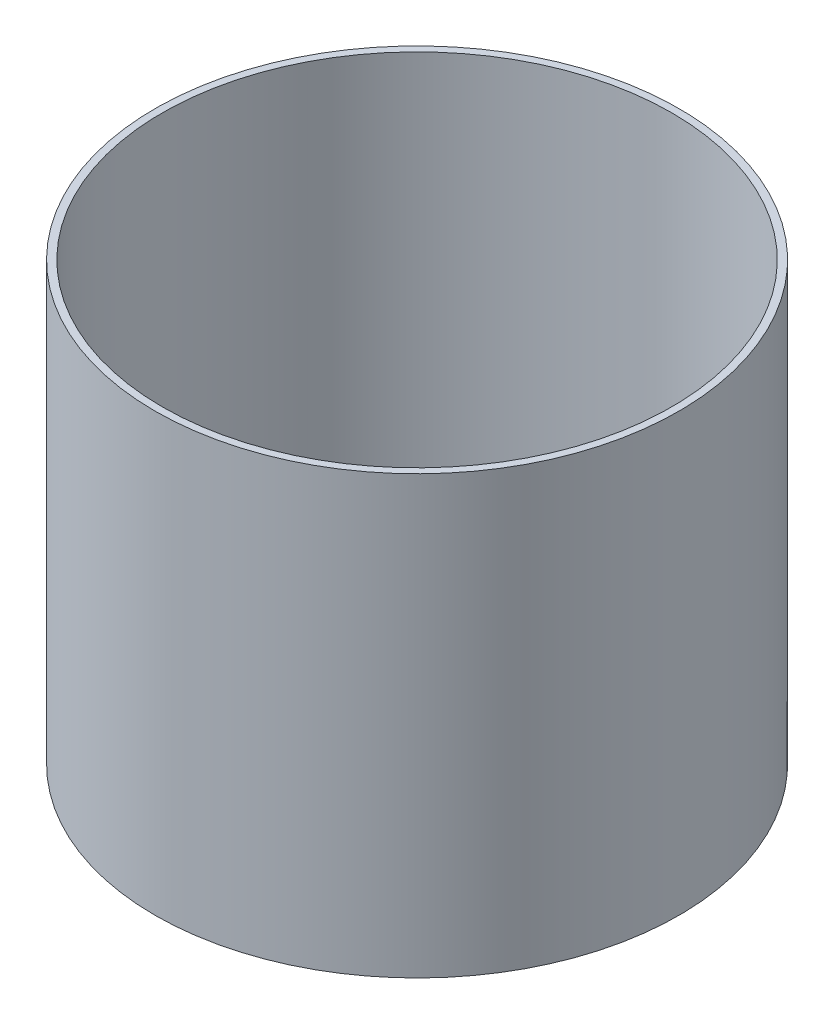
SolidWorks part; units mm, degrees
ref_plane "Front Plane" through (0, 0, 0) normal (0, 0, 1) x (1, 0, 0)
ref_plane "Top Plane" through (0, 0, 0) normal (0, 1, 0) x (1, 0, 0)
ref_plane "Right Plane" through (0, 0, 0) normal (1, 0, 0) x (0, 0, -1)
sketch "Sketch1" plane through (0, 0, 0) normal (0, 1, 0) x (1, 0, 0)
  circle A0 centre (0, 0) radius 35
  circle A1 centre (0, 0) radius 36
  dimension "D1" = 70
  dimension "D2" = 72
extrude "Boss-Extrude1" add sketch "Sketch1" along normal blind 60
